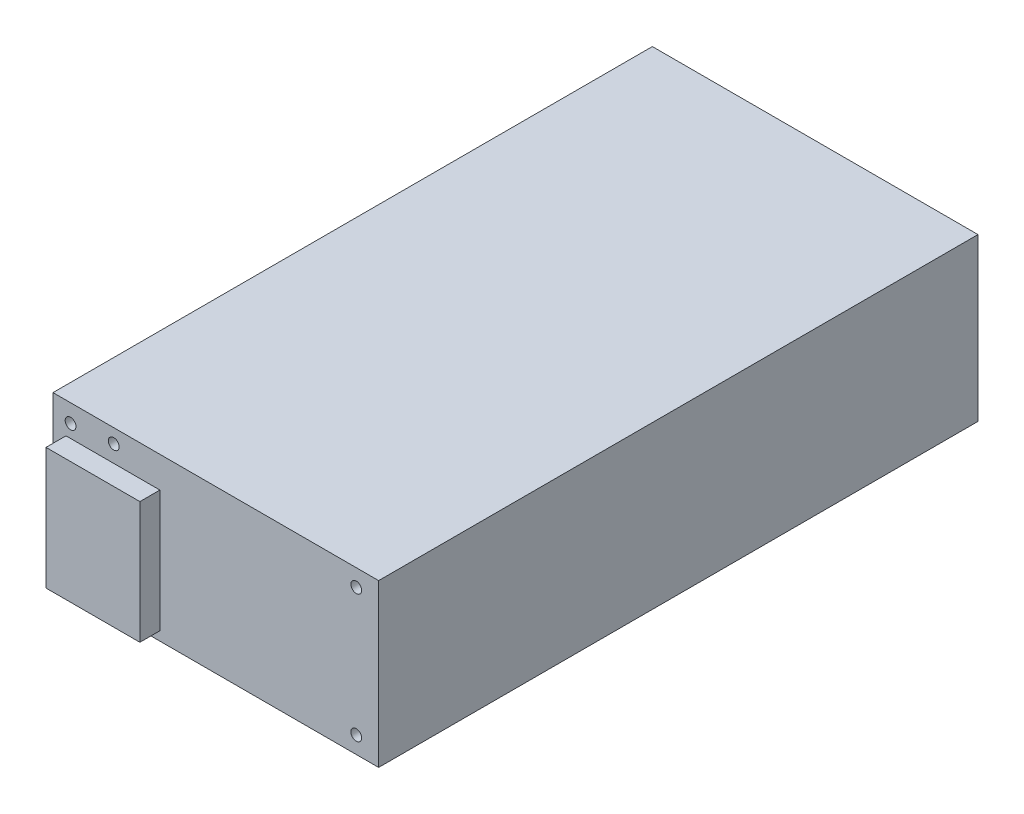
SolidWorks part; units mm, degrees
material "Galvanized Steel"
ref_plane "Front Plane" through (0, 0, 0) normal (0, 0, 1) x (1, 0, 0)
ref_plane "Top Plane" through (0, 0, 0) normal (0, 1, 0) x (1, 0, 0)
ref_plane "Right Plane" through (0, 0, 0) normal (1, 0, 0) x (0, 0, -1)
sketch "Sketch1" plane through (0, 0, 0) normal (1, 0, 0) x (0, 0, -1)
  line L0 (0, 0) -> (0, 40.5)
  line L1 (0, 40.5) -> (150, 40.5)
  line L4 (150, 40.5) -> (150, 0)
  line L5 (150, 0) -> (0, 0)
  point P5 (0, 0)
  point P7 (0, 0)
  dimension "D1" = 150
  dimension "D2" = 40.5
extrude "main-body" add sketch "Sketch1" along normal blind 81.5
hole_wizard "#6-32 Tapped Hole2" positions "Sketch5" profile "Sketch6" tap size "#6-32" standard "ANSI Inch"
sketch "Sketch5" plane through (0, 0, 0) normal (0, 0, 1) x (1, 0, 0)
  line L0 (75.9, 36.25) -> (75.9, 4.25) construction
  line L2 (81.5, 40.5) -> (81.5, 0) construction
  line L3 (0, 40.5) -> (0, 0) construction
  line L5 (81.5, 0) -> (0, 0) construction
  point P0 (4.4, 36)
  point P2 (15.2, 37)
  point P4 (75.9, 36.25)
  point P6 (75.9, 4.25)
  point P15 (81.5, 20.25)
  point P16 (75.9, 20.25)
  dimension "D1" = 5.6
  dimension "D2" = 32
  dimension "D3" = 15.2
  dimension "D4" = 4.4
  dimension "D5" = 37
  dimension "D6" = 36
sketch "Sketch6" plane through (4.4, 36, 0) normal (1, 0, 0) x (0, -1, 0)
  line L0 (0, 0) -> (0, 5.8127)
  line L1 (0, 5.8127) -> (1.3525, 5)
  line L2 (1.3525, 5) -> (1.3525, 0)
  line L5 (1.3525, 0) -> (0, 0)
  line L10 (0, 5.8127) -> (-1.3525, 5) construction
  line L11 (0, -6.35) -> (0, 107.95) construction
  dimension "Tap Drill Dia." = 2.7051
  dimension "Tap Drill Depth" = 5
  dimension "Drill Angle" = 118
sketch "Sketch7" plane through (0, 0, 0) normal (0, 0, 1) x (1, 0, 0)
  line L0 (81.5, 0) -> (0, 0) construction
  line L1 (3.25, 2.25) -> (26.75, 2.25)
  line L2 (3.25, 2.25) -> (3.25, 32.75)
  line L3 (3.25, 32.75) -> (26.75, 32.75)
  line L4 (26.75, 2.25) -> (26.75, 32.75)
  line L5 (0, 40.5) -> (0, 0) construction
  point P4 (3.25, 17.5)
  point P7 (15, 2.25)
  dimension "D1" = 23.5
  dimension "D2" = 30.5
  dimension "D3" = 17.5
  dimension "D4" = 15
extrude "Boss-Extrude1" add sketch "Sketch7" along normal blind 5
